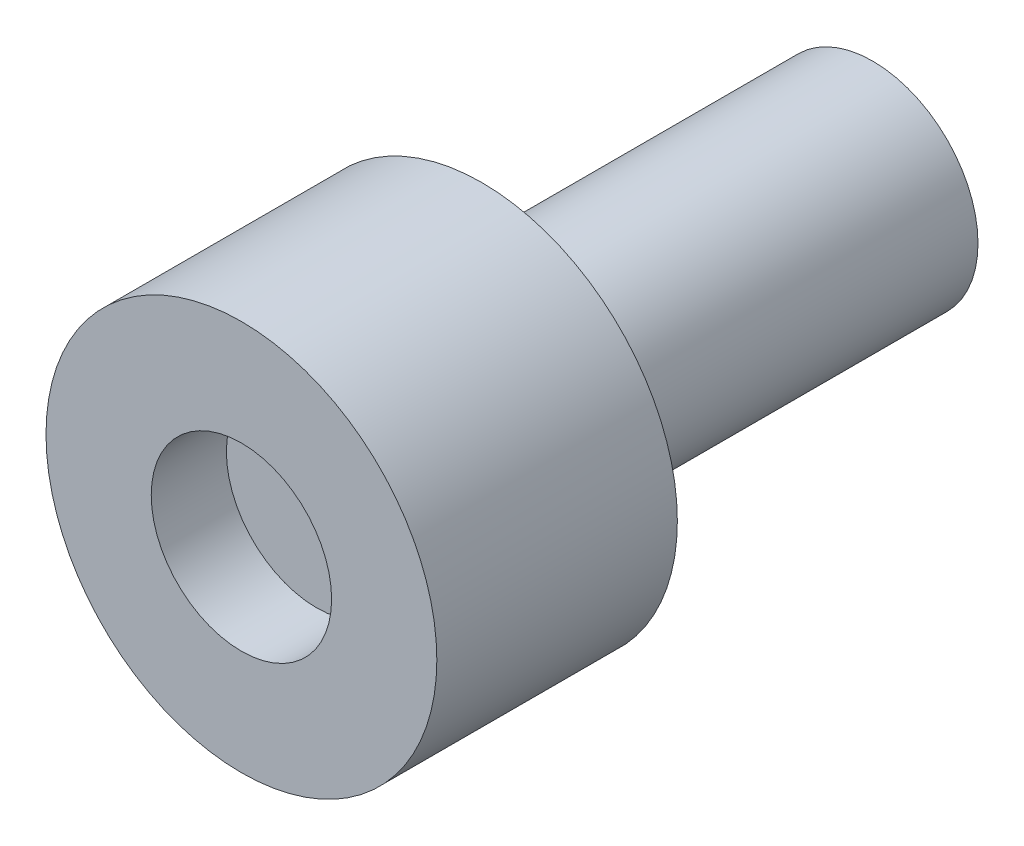
SolidWorks part; units mm, degrees
ref_plane "Front Plane" through (0, 0, 0) normal (0, 0, 1) x (1, 0, 0)
ref_plane "Top Plane" through (0, 0, 0) normal (0, 1, 0) x (1, 0, 0)
ref_plane "Right Plane" through (0, 0, 0) normal (1, 0, 0) x (0, 0, -1)
ref_plane "Plane1" through (0, 0, 0) normal (0, -1, 0) x (1, 0, 0)
sketch "Sketch1" plane through (0, 0, 0) normal (0, -1, 0) x (1, 0, 0)
  line L0 (3, 5.5) -> (0, 5.5)
  line L1 (0, 5.5) -> (0, -13)
  line L2 (0, -13) -> (3.5, -13)
  line L3 (3.5, -13) -> (3.5, 0)
  line L4 (3.5, 0) -> (6.5, 0)
  line L5 (6.5, 0) -> (6.5, 8)
  line L6 (6.5, 8) -> (3, 8)
  line L7 (3, 8) -> (3, 5.5)
  line L8 (0, 8) -> (0, -13) construction
revolve "Revolve1" add sketch "Sketch1" angle 360 about L8
